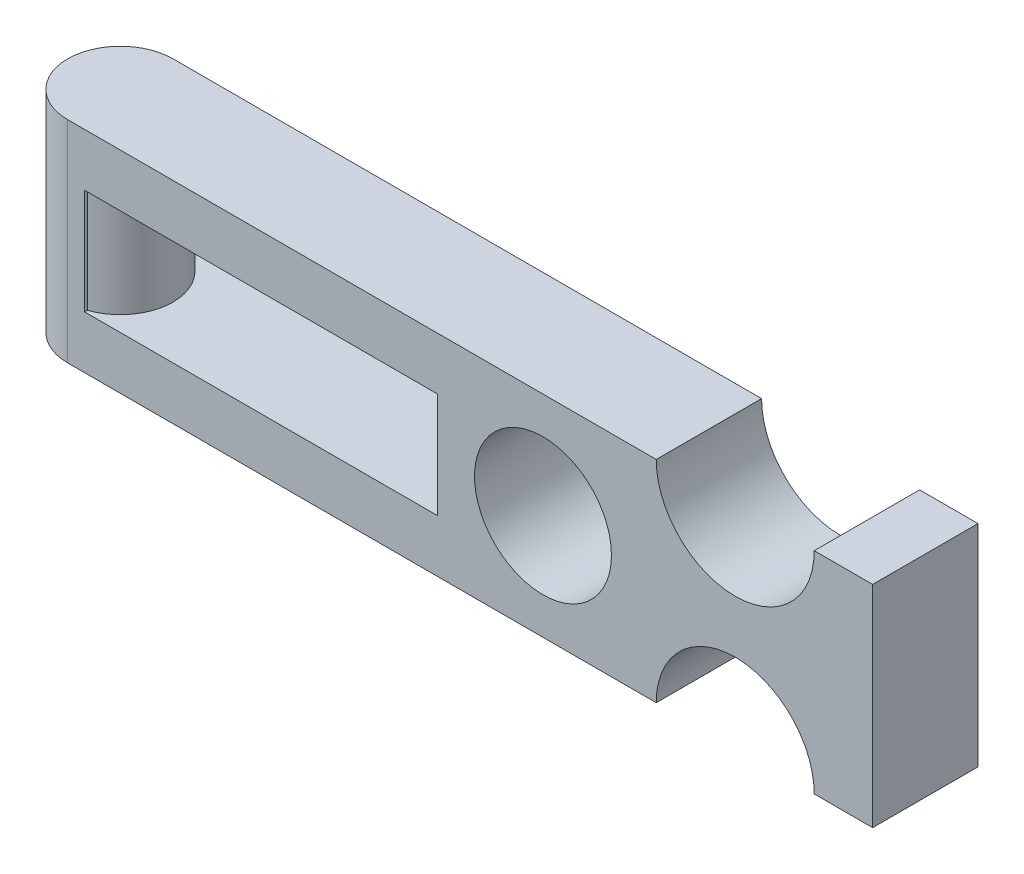
SolidWorks part; units mm, degrees
ref_plane "Front Plane" through (0, 0, 0) normal (0, 0, 1) x (1, 0, 0)
ref_plane "Top Plane" through (0, 0, 0) normal (0, 1, 0) x (1, 0, 0)
ref_plane "Right Plane" through (0, 0, 0) normal (1, 0, 0) x (0, 0, -1)
sketch "Sketch1" plane through (0, 0, 0) normal (0, 0, 1) x (1, 0, 0)
  line L0 (89.9992, 12.7) -> (97.04, 12.7)
  line L1 (0, 12.7) -> (70.9492, 12.7)
  line L2 (0, 12.7) -> (0, -12.7)
  line L3 (0, -12.7) -> (70.9492, -12.7)
  line L4 (97.04, 12.7) -> (97.04, -12.7)
  line L5 (89.9992, -12.7) -> (97.04, -12.7)
  line L7 (2.0371, 6.35) -> (44.5666, 6.35)
  line L8 (2.0371, 6.35) -> (2.0371, -6.35)
  line L9 (2.0371, -6.35) -> (44.5666, -6.35)
  line L10 (44.5666, 6.35) -> (44.5666, -6.35)
  circle A0 centre (57.297, 0) radius 8.255
  arc A1 (70.9492, 12.7) -> (89.9992, 12.7) centre (80.4742, 12.7) ccw
  arc A2 (89.9992, -12.7) -> (70.9492, -12.7) centre (80.4742, -12.7) ccw
  point P4 (0, 0)
  point P12 (2.0371, 0)
  dimension "D3" = 16.51
  dimension "D5" = 19.05
  dimension "D6" = 80.4742
  dimension "D1" = 25.4
  dimension "D2" = 57.297
  dimension "D4" = 97.04
  dimension "D7" = 12.7
  dimension "D8" = 42.5295
  dimension "D9" = 2.0371
extrude "Boss-Extrude1" add sketch "Sketch1" along normal blind 12.7
sketch "Sketch2" plane through (0, 12.7, 0) normal (0, 1, 0) x (1, 0, 0)
  line L0 (0, -12.7) -> (0, 0) construction
  line L1 (70.9492, -12.7) -> (0, -12.7) construction
  circle A0 centre (0, -6.35) radius 6.35
extrude "Boss-Extrude2" add sketch "Sketch2" against normal through all
